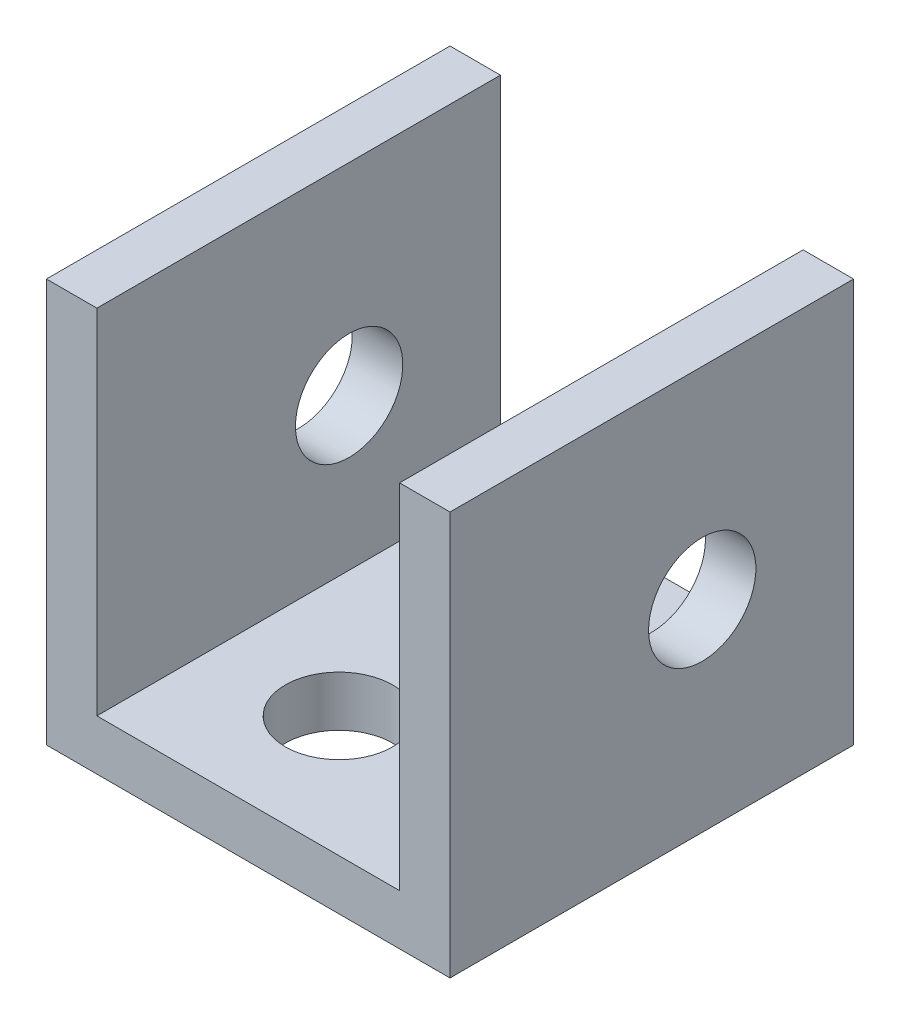
SolidWorks part; units mm, degrees
material "6061-T6 (SS)"
ref_plane "Front" through (0, 0, 0) normal (0, 0, 1) x (1, 0, 0)
ref_plane "Top" through (0, 0, 0) normal (0, 1, 0) x (1, 0, 0)
ref_plane "Right" through (0, 0, 0) normal (1, 0, 0) x (0, 0, -1)
sketch "Sketch1" plane through (0, 0, 0) normal (0, 1, 0) x (1, 0, 0)
  line L1 (-12.7, -12.7) -> (12.7, -12.7)
  line L2 (-12.7, -12.7) -> (-12.7, 12.7)
  line L3 (-12.7, 12.7) -> (12.7, 12.7)
  line L4 (12.7, -12.7) -> (12.7, 12.7)
  line L5 (-12.7, -12.7) -> (12.7, 12.7) construction
  line L6 (-12.7, 12.7) -> (12.7, -12.7) construction
  point P0 (0, 0)
  dimension "D1" = 25.4
  dimension "D2" = 25.4
extrude "Boss-Extrude1" add sketch "Sketch1" along normal blind 3.175
sketch "Sketch2" plane through (0, 3.175, 0) normal (0, 1, 0) x (1, 0, 0)
  line L0 (-12.7, 12.7) -> (-12.7, -12.7)
  line L1 (-12.7, -12.7) -> (-9.525, -12.7)
  line L2 (-12.7, -12.7) -> (12.7, -12.7) construction
  line L3 (-9.525, -12.7) -> (-9.525, 12.7)
  line L4 (12.7, 12.7) -> (-12.7, 12.7) construction
  line L5 (-9.525, 12.7) -> (-12.7, 12.7)
  line L6 (12.7, 12.7) -> (9.525, 12.7)
  line L7 (9.525, 12.7) -> (9.525, -12.7)
  line L8 (9.525, -12.7) -> (12.7, -12.7)
  line L9 (12.7, -12.7) -> (12.7, 12.7)
  dimension "D1" = 3.175
extrude "Boss-Extrude2" add sketch "Sketch2" along normal blind 22.225
sketch "Sketch6" plane through (0, 3.175, 0) normal (0, 1, 0) x (1, 0, 0)
  line L0 (9.525, 12.7) -> (-9.525, 12.7) construction
  line L1 (9.525, 12.7) -> (9.525, -12.7) construction
  line L2 (-9.525, -12.7) -> (-9.525, 12.7) construction
  line L3 (-9.525, -12.7) -> (9.525, -12.7) construction
  point P0 (1.905, 5.08)
  point P2 (-1.905, -5.08)
  dimension "D1" = 7.62
  dimension "D2" = 7.62
  dimension "D3" = 7.62
  dimension "D4" = 7.62
hole_wizard "1/4 Clearance Hole2" positions "Sketch6" profile "Sketch5" hole size "1/4" standard "ANSI Inch" end condition through all
sketch "Sketch5" plane through (1.905, 3.175, -5.08) normal (1, 0, 0) x (0, 0, 1)
  line L0 (0, 0) -> (0, 3.175)
  line L1 (0, 3.175) -> (3.3782, 3.175)
  line L2 (3.3782, 3.175) -> (3.3782, 0)
  line L5 (3.3782, 0) -> (0, 0)
  line L11 (0, -6.35) -> (0, 107.95) construction
  dimension "Thru Hole Dia." = 6.7564
  dimension "Thru Hole Depth" = 3.175
sketch "Sketch9" plane through (-12.7, 0, 0) normal (-1, 0, 0) x (0, 0, 1)
  line L0 (-12.7, 25.4) -> (12.7, 25.4) construction
  line L1 (-12.7, 25.4) -> (-12.7, 0) construction
  point P0 (-3.175, 12.7)
  dimension "D1" = 12.7
  dimension "D2" = 9.525
hole_wizard "1/4 Clearance Hole1" positions "Sketch9" profile "Sketch8" hole size "1/4" standard "ANSI Inch" end condition through all
sketch "Sketch8" plane through (-12.7, 12.7, -3.175) normal (0, 1, 0) x (0, 0, 1)
  line L0 (0, 0) -> (0, 25.4)
  line L1 (0, 25.4) -> (3.3782, 25.4)
  line L2 (3.3782, 25.4) -> (3.3782, 0)
  line L5 (3.3782, 0) -> (0, 0)
  line L11 (0, -6.35) -> (0, 107.95) construction
  dimension "Thru Hole Dia." = 6.7564
  dimension "Thru Hole Depth" = 25.4
